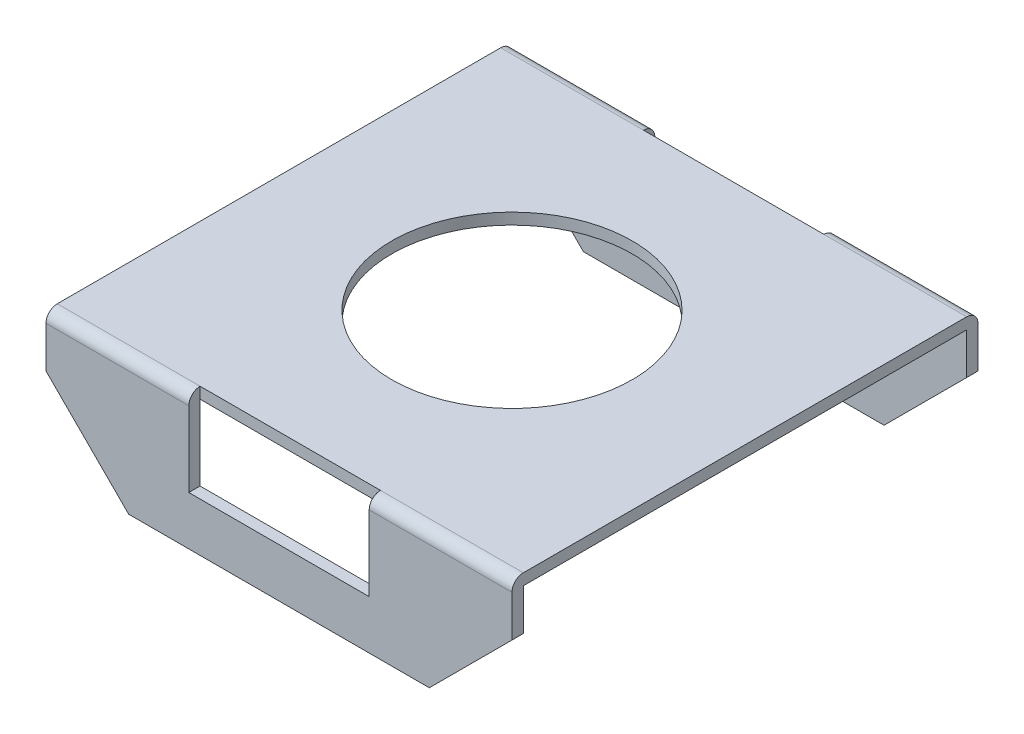
SolidWorks part; units mm, degrees
ref_plane "Front Plane" through (0, 0, 0) normal (0, 0, 1) x (1, 0, 0)
ref_plane "Top Plane" through (0, 0, 0) normal (0, 1, 0) x (1, 0, 0)
ref_plane "Right Plane" through (0, 0, 0) normal (1, 0, 0) x (0, 0, -1)
sketch "Sketch1" plane through (0, 0, 0) normal (1, 0, 0) x (0, 0, -1)
  line L0 (-3.1, 0.2) -> (-3.1, 2)
  line L1 (-3.1, 2) -> (3.1, 2)
  line L2 (3.1, 2) -> (3.1, 0.2)
  line L3 (3.41, 0) -> (-3.41, 0) construction
  line L4 (0, 0.99) -> (0, -0.99) construction
  dimension "D1" = 2
  dimension "D2" = 6.2
  dimension "D3" = 3.1
  dimension "D4" = 1.8
extrude "Extrude-Thin3" add sketch "Sketch1" along normal mid plane 6.2 thin
sketch "Sketch2" plane through (0, 0, 0) normal (0, 0, 1) x (1, 0, 0)
  line L1 (-1.2, 1.85) -> (1.2, 1.85)
  line L2 (-1.2, 1.85) -> (-1.2, 0.85)
  line L3 (-1.2, 0.85) -> (1.2, 0.85)
  line L4 (1.2, 1.85) -> (1.2, 0.85)
  line L5 (-3.1, 1.3) -> (-2, 0.2)
  line L6 (3.1, 0.2) -> (3.1, 1.3)
  line L7 (3.1, 0.2) -> (-3.1, 0.2) construction
  line L8 (-2, 0.2) -> (-3.1, 0.2)
  line L9 (-3.1, 0.2) -> (-3.1, 1.3)
  line L10 (-3.1, 0.2) -> (-3.1, 2) construction
  line L11 (3.1, 1.3) -> (2, 0.2)
  line L12 (3.1, 0.2) -> (3.1, 2) construction
  line L13 (2, 0.2) -> (3.1, 0.2)
  line L14 (0, -0.99) -> (0, 0.99) construction
  dimension "D1" = 4
  dimension "D2" = 2
  dimension "D3" = 45
  dimension "D4" = 45
  dimension "D5" = 2.4
  dimension "D6" = 1.2
extrude "Cut-Extrude1" cut sketch "Sketch2" against normal through all and the other way through all
sketch "Sketch3" plane through (0, 2, 0) normal (0, 1, 0) x (1, 0, 0)
  line L1 (-1.2, 3.1) -> (1.2, 3.1)
  line L2 (-1.2, 3.1) -> (-1.2, 2.95)
  line L3 (-1.2, 2.95) -> (1.2, 2.95)
  line L4 (1.2, 3.1) -> (1.2, 2.95)
  line L5 (-1.2, -3.1) -> (1.2, -3.1)
  line L6 (-1.2, -3.1) -> (-1.2, -2.95)
  line L7 (-1.2, -2.95) -> (1.2, -2.95)
  line L8 (1.2, -3.1) -> (1.2, -2.95)
extrude "Cut-Extrude2" cut sketch "Sketch3" against normal blind 1
fillet "Fillet1" radius 0.15 4 edges at (-2.15, 2, -3.1) (2.15, 2, -3.1) (-2.15, 2, 3.1) (2.15, 2, 3.1)
sketch "Sketch4" plane through (0, 2, 0) normal (0, 1, 0) x (1, 0, 0)
  circle A0 centre (0, 0) radius 1.6
  dimension "D1" = 3.2
extrude "Cut-Extrude3" cut sketch "Sketch4" against normal blind 1
